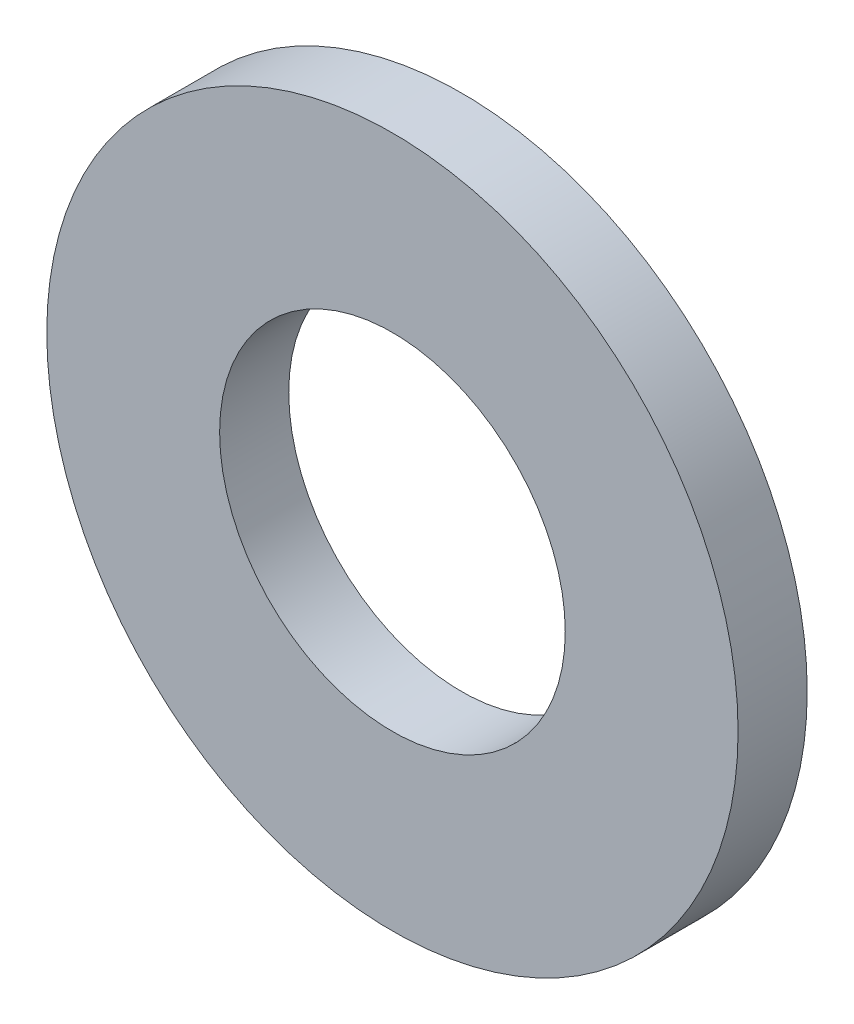
SolidWorks part; units mm, degrees
ref_plane "Front Plane" through (0, 0, 0) normal (0, 0, 1) x (1, 0, 0)
ref_plane "Top Plane" through (0, 0, 0) normal (0, 1, 0) x (1, 0, 0)
ref_plane "Right Plane" through (0, 0, 0) normal (1, 0, 0) x (0, 0, -1)
sketch "Sketch1" plane through (0, 0, 0) normal (0, 0, 1) x (1, 0, 0)
  circle A0 centre (0, 0) radius 10
extrude "Boss-Extrude1" add sketch "Sketch1" along normal blind 2
sketch "Sketch2" plane through (0, 0, 2) normal (0, 0, 1) x (1, 0, 0)
  circle A0 centre (0, 0) radius 5
extrude "Cut-Extrude1" cut sketch "Sketch2" against normal blind 4
